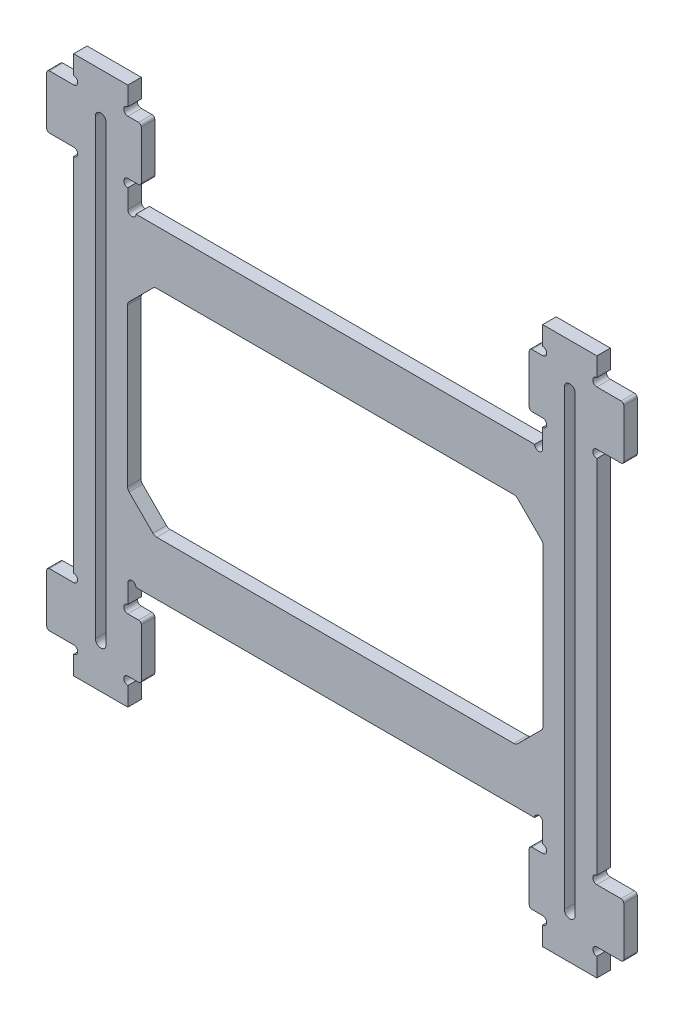
SolidWorks part; units mm, degrees
ref_plane "前视基准面" through (0, 0, 0) normal (0, 0, 1) x (1, 0, 0)
ref_plane "上视基准面" through (0, 0, 0) normal (0, 1, 0) x (1, 0, 0)
ref_plane "右视基准面" through (0, 0, 0) normal (1, 0, 0) x (0, 0, -1)
sketch "草图1" plane through (0, 0, 0) normal (0, 0, 1) x (1, 0, 0)
  line L1 (-48.55, -50) -> (48.55, -50)
  line L2 (-48.55, -50) -> (-48.55, 50)
  line L3 (-48.55, 50) -> (48.55, 50)
  line L4 (48.55, -50) -> (48.55, 50)
  line L5 (-48.55, -50) -> (48.55, 50) construction
  line L6 (-48.55, 50) -> (48.55, -50) construction
  point P0 (0, 0)
  dimension "D1" = 97.1
  dimension "D2" = 100
extrude "凸台-拉伸1" add sketch "草图1" along normal mid plane 2.5
sketch "草图2" plane through (0, 0, 1.25) normal (0, 0, 1) x (1, 0, 0)
  line L0 (-48.55, 50) -> (-48.55, -50) construction
  line L1 (-43.55, -45) -> (-53.55, -45)
  line L2 (-43.55, -45) -> (-43.55, -35)
  line L3 (-43.55, -35) -> (-53.55, -35)
  line L4 (-53.55, -45) -> (-53.55, -35)
  line L5 (-43.55, -45) -> (-53.55, -35) construction
  line L6 (-43.55, -35) -> (-53.55, -45) construction
  line L7 (0, 50) -> (0, -50) construction
  line L8 (-43.55, 45) -> (-53.55, 45)
  line L9 (-43.55, 45) -> (-43.55, 35)
  line L10 (-43.55, 35) -> (-53.55, 35)
  line L11 (-53.55, 45) -> (-53.55, 35)
  line L12 (-43.55, 45) -> (-53.55, 35) construction
  line L13 (-43.55, 35) -> (-53.55, 45) construction
  line L14 (48.55, 50) -> (-48.55, 50) construction
  line L15 (-48.55, -50) -> (48.55, -50) construction
  line L16 (-48.55, -40) -> (-48.55, 40) construction
  line L17 (43.55, -35) -> (53.55, -35)
  line L18 (53.55, -45) -> (53.55, -35)
  line L19 (43.55, -45) -> (53.55, -45)
  line L20 (43.55, -45) -> (43.55, -35)
  line L21 (43.55, 35) -> (53.55, 35)
  line L22 (53.55, 45) -> (53.55, 35)
  line L23 (43.55, 45) -> (53.55, 45)
  line L24 (43.55, 45) -> (43.55, 35)
  point P0 (-48.55, -40)
  point P7 (-48.55, 40)
  point P20 (-48.55, 0)
  dimension "D1" = 80
  dimension "D2" = 10
  dimension "D3" = 10
extrude "凸台-拉伸2" add sketch "草图2" against normal blind 2.5
sketch "草图5" plane through (0, 0, 1.25) normal (0, 0, 1) x (1, 0, 0)
  line L0 (-38.5, 50) -> (-38.5, 45)
  line L1 (48.55, 50) -> (-48.55, 50) construction
  line L2 (-38.5, 45) -> (-36, 45)
  line L3 (-36, 45) -> (-36, 35)
  line L4 (-36, 35) -> (-38.5, 35)
  line L5 (-38.5, 35) -> (-38.5, 30)
  line L6 (-38.5, 30) -> (38.5, 30)
  line L7 (38.5, 30) -> (38.5, 35)
  line L8 (38.5, 35) -> (36, 35)
  line L9 (36, 35) -> (36, 45)
  line L10 (36, 45) -> (38.5, 45)
  line L11 (38.5, 45) -> (38.5, 50)
  line L12 (-48.55, 0) -> (48.55, 0) construction
  line L13 (-48.55, 35) -> (-48.55, -35) construction
  line L14 (48.55, -35) -> (48.55, 35) construction
  line L15 (-48.55, 45) -> (-53.55, 45) construction
  line L16 (-53.55, 45) -> (-53.55, 35) construction
  line L17 (-38.5, 50) -> (38.5, 50)
  line L18 (-38.5, -50) -> (-38.5, -45)
  line L19 (-38.5, -45) -> (-36, -45)
  line L20 (-36, -45) -> (-36, -35)
  line L21 (-36, -35) -> (-38.5, -35)
  line L22 (-38.5, -35) -> (-38.5, -30)
  line L23 (-38.5, -30) -> (38.5, -30)
  line L24 (38.5, -30) -> (38.5, -35)
  line L25 (38.5, -35) -> (36, -35)
  line L26 (36, -35) -> (36, -45)
  line L27 (36, -45) -> (38.5, -45)
  line L28 (38.5, -45) -> (38.5, -50)
  line L29 (-38.5, -50) -> (38.5, -50)
  point P15 (0, 30)
  dimension "D1" = 10.05
  dimension "D2" = 5
  dimension "D3" = 2.5
extrude "切除-拉伸2" cut sketch "草图5" against normal through all
sketch "草图3" plane through (0, 0, 1.25) normal (0, 0, 1) x (1, 0, 0)
  line L0 (-48.55, 35) -> (-48.55, -35) construction
  line L1 (-48.55, 50) -> (-48.55, 45) construction
  line L2 (-48.55, -45) -> (-48.55, -50) construction
  line L3 (48.55, -35) -> (48.55, 35) construction
  line L4 (48.55, -50) -> (48.55, -45) construction
  line L5 (48.55, 45) -> (48.55, 50) construction
  line L6 (-38.5, 50) -> (-38.5, 45) construction
  line L7 (-38.5, 35) -> (-38.5, 30) construction
  line L8 (-38.5, 30) -> (38.5, 30) construction
  line L9 (38.5, -30) -> (-38.5, -30) construction
  line L10 (-38.5, -30) -> (-38.5, -35) construction
  line L11 (-38.5, -45) -> (-38.5, -50) construction
  line L12 (38.5, -50) -> (38.5, -45) construction
  line L13 (38.5, -35) -> (38.5, -30) construction
  line L14 (38.5, 30) -> (38.5, 35) construction
  line L15 (38.5, 45) -> (38.5, 50) construction
  circle A0 centre (-48.55, 34.25) radius 0.75
  circle A1 centre (-48.55, 45.75) radius 0.75
  circle A2 centre (-48.55, -34.25) radius 0.75
  circle A3 centre (-48.55, -45.75) radius 0.75
  circle A4 centre (48.55, -34.25) radius 0.75
  circle A5 centre (48.55, -45.75) radius 0.75
  circle A6 centre (48.55, 34.25) radius 0.75
  circle A7 centre (48.55, 45.75) radius 0.75
  circle A8 centre (-38.5, 45.75) radius 0.75
  circle A9 centre (-38.5, 34.25) radius 0.75
  circle A10 centre (-37.75, 30) radius 0.75
  circle A11 centre (-37.75, -30) radius 0.75
  circle A12 centre (-38.5, -34.25) radius 0.75
  circle A13 centre (-38.5, -45.75) radius 0.75
  circle A14 centre (38.5, -45.75) radius 0.75
  circle A15 centre (38.5, -34.25) radius 0.75
  circle A16 centre (37.75, -30) radius 0.75
  circle A17 centre (37.75, 30) radius 0.75
  circle A18 centre (38.5, 34.25) radius 0.75
  circle A19 centre (38.5, 45.75) radius 0.75
  dimension "D1" = 1.5
extrude "切除-拉伸1" cut sketch "草图3" against normal through all
fillet "圆角1" radius 0.5 16 edges at (53.55, 45, 0) (53.55, 35, 0) (53.55, -35, 0) (53.55, -45, 0) (-53.55, -45, 0) (-53.55, -35, 0) (-53.55, 45, 0) (-53.55, 35, 0) (36, -45, 0) (36, -35, 0) (-36, -35, 0) (-36, -45, 0) (36, 35, 0) (36, 45, 0) (-36, 35, 0) (-36, 45, 0)
sketch "草图6" plane through (0, 0, 1.25) normal (0, 0, 1) x (1, 0, 0)
  line L0 (-37, 30) -> (37, 30) construction
  line L1 (38.55, -20) -> (-38.55, -20)
  line L2 (38.55, -20) -> (38.55, 20)
  line L3 (38.55, 20) -> (-38.55, 20)
  line L4 (-38.55, -20) -> (-38.55, 20)
  line L5 (38.55, -20) -> (-38.55, 20) construction
  line L6 (38.55, 20) -> (-38.55, -20) construction
  line L7 (48.55, -33.5) -> (48.55, 33.5) construction
  point P0 (0, 0)
  dimension "D1" = 10
  dimension "D2" = 10
extrude "切除-拉伸3" cut sketch "草图6" against normal through all
chamfer "倒角1" distance 5 angle 45 4 edges at (-38.55, -20, 0) (38.55, -20, 0) (38.55, 20, 0) (-38.55, 20, 0)
fillet "圆角2" radius 1 8 edges at (33.55, -20, 0) (38.55, -15, 0) (38.55, 15, 0) (33.55, 20, 0) (-38.55, 15, 0) (-38.55, -15, 0) (-33.55, -20, 0) (-33.55, 20, 0)
sketch "草图7" plane through (0, 0, 1.25) normal (0, 0, 1) x (1, 0, 0)
  line L0 (-43.525, -42) -> (-43.525, 42) construction
  line L1 (-44.525, -42) -> (-44.525, 42)
  line L2 (-42.525, -42) -> (-42.525, 42)
  line L3 (-38.5, 50) -> (-48.55, 50) construction
  line L4 (0, 30) -> (0, -30) construction
  line L5 (-37, 30) -> (37, 30) construction
  line L6 (37, -30) -> (-37, -30) construction
  line L7 (43.525, -42) -> (43.525, 42) construction
  line L8 (44.525, -42) -> (44.525, 42)
  line L9 (42.525, -42) -> (42.525, 42)
  arc A0 (-44.525, -42) -> (-42.525, -42) centre (-43.525, -42) ccw
  arc A1 (-42.525, 42) -> (-44.525, 42) centre (-43.525, 42) ccw
  arc A2 (44.525, -42) -> (42.525, -42) centre (43.525, -42) cw
  arc A3 (42.525, 42) -> (44.525, 42) centre (43.525, 42) cw
  point P2 (-43.525, 0)
  point P11 (-43.525, 50)
  point P19 (43.525, 0)
  dimension "D1" = 1
  dimension "D2" = 8
extrude "切除-拉伸4" cut sketch "草图7" against normal through all
